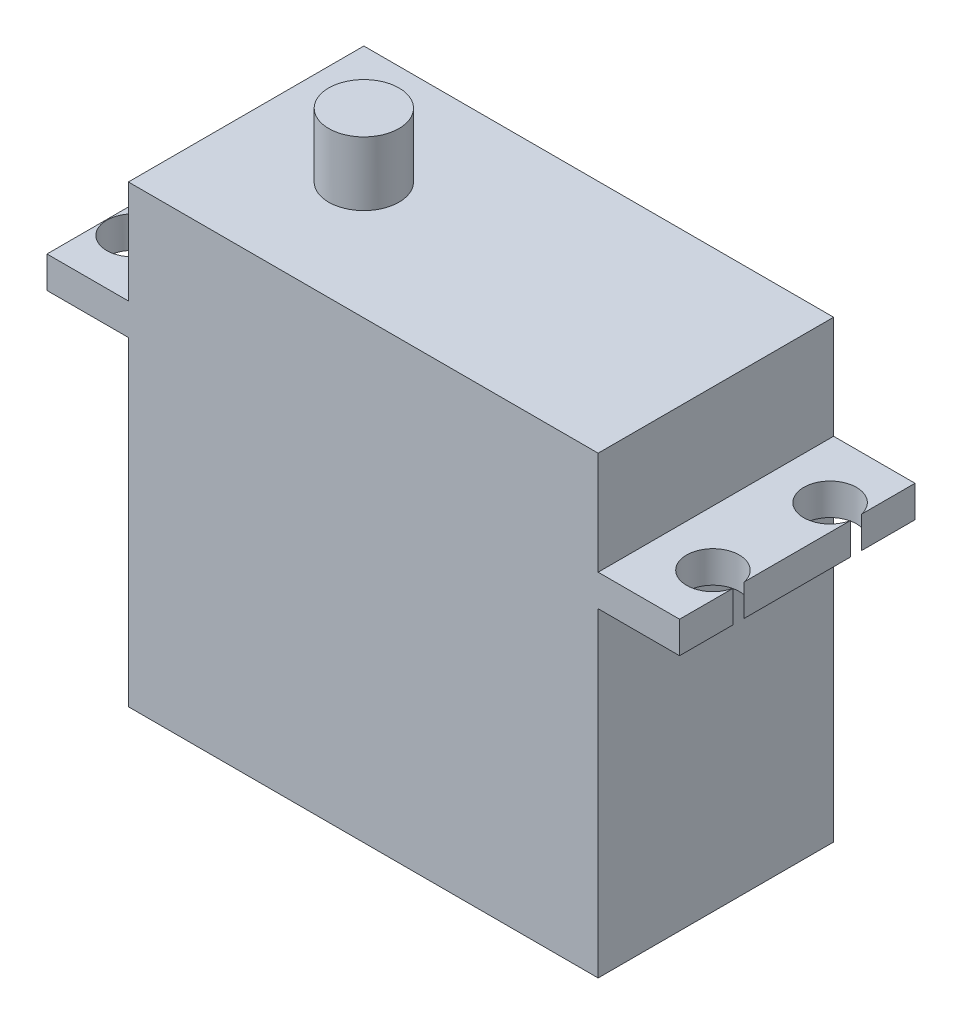
SolidWorks part; units mm, degrees
ref_plane "正面(Front)" through (0, 0, 0) normal (0, 0, 1) x (1, 0, 0)
ref_plane "平面(Top)" through (0, 0, 0) normal (0, 1, 0) x (1, 0, 0)
ref_plane "右側面(Right)" through (0, 0, 0) normal (1, 0, 0) x (0, 0, -1)
sketch "ｽｹｯﾁ1" plane through (0, 0, 0) normal (0, 1, 0) x (1, 0, 0)
  line L1 (-20.05, 10.05) -> (20.05, 10.05)
  line L2 (-20.05, 10.05) -> (-20.05, -10.05)
  line L3 (-20.05, -10.05) -> (20.05, -10.05)
  line L4 (20.05, 10.05) -> (20.05, -10.05)
  line L5 (-20.05, 10.05) -> (20.05, -10.05) construction
  line L6 (-20.05, -10.05) -> (20.05, 10.05) construction
  point P0 (0, 0)
  dimension "D1" = 20.1
  dimension "D2" = 40.1
extrude "ﾎﾞｽ - 押し出し2" add sketch "ｽｹｯﾁ1" along normal blind 38.8
ref_plane "平面1" through (0, 44.25, 0) normal (0, -1, 0) x (-1, 0, 0)
ref_plane "平面2" through (0, 30, 0) normal (0, -1, 0) x (-1, 0, 0)
sketch "ｽｹｯﾁ2" plane through (0, 30, 0) normal (0, -1, 0) x (-1, 0, 0)
  line L0 (20.05, -10.05) -> (-20.05, -10.05) construction
  line L1 (-27, 10.05) -> (27, 10.05)
  line L2 (-27, 10.05) -> (-27, -10.05)
  line L3 (-27, -10.05) -> (27, -10.05)
  line L4 (27, 10.05) -> (27, -10.05)
  line L5 (-27, 10.05) -> (27, -10.05) construction
  line L6 (-27, -10.05) -> (27, 10.05) construction
  point P0 (0, 0)
  point P6 (27, -11.0352)
  dimension "D1" = 54
extrude "ﾎﾞｽ - 押し出し3" add sketch "ｽｹｯﾁ2" along normal offset from surface (2.7 mm away) 27.3 up to face at (0, 0, 0)
sketch "ｽｹｯﾁ4" plane through (0, 38.8, 0) normal (0, 1, 0) x (1, 0, 0)
  line L0 (0, 0) -> (-30.5837, 0) construction
  circle A0 centre (-10, 0) radius 3
  point P5 (-9.7713, 0)
  dimension "D1" = 10
  dimension "D2" = 6
extrude "ﾎﾞｽ - 押し出し4" add sketch "ｽｹｯﾁ4" along normal up to surface (5.45 mm away) up to plane "平面1"
sketch "ｽｹｯﾁ5" plane through (0, 30, 0) normal (0, 1, 0) x (1, 0, 0)
  line L0 (0, 0) -> (33.7734, 0) construction
  line L1 (0, 0) -> (0, 17.3245) construction
  circle A0 centre (24.8, 5) radius 2.25
  circle A1 centre (24.8, -5) radius 2.25
  circle A2 centre (-24.7, 5) radius 2.25
  circle A3 centre (-24.7, -5) radius 2.25
  point P10 (0, 0)
  dimension "D1" = 24.8
  dimension "D3" = 4.5
  dimension "D4" = 24.7
  dimension "D2" = 10
extrude "ｶｯﾄ - 押し出し1" cut sketch "ｽｹｯﾁ5" against normal through all
sketch "ｽｹｯﾁ6" plane through (-20.05, 0, 0) normal (-1, 0, 0) x (0, 0, 1)
  line L1 (-4, 11) -> (4, 11)
  line L2 (-4, 11) -> (-4, 7)
  line L3 (-4, 7) -> (4, 7)
  line L4 (4, 11) -> (4, 7)
  line L5 (-4, 11) -> (4, 7) construction
  line L6 (-4, 7) -> (4, 11) construction
  point P0 (0, 9)
  dimension "D1" = 7
  dimension "D2" = 4
  dimension "D3" = 8
extrude "ﾎﾞｽ - 押し出し5" add sketch "ｽｹｯﾁ6" along normal blind 3
